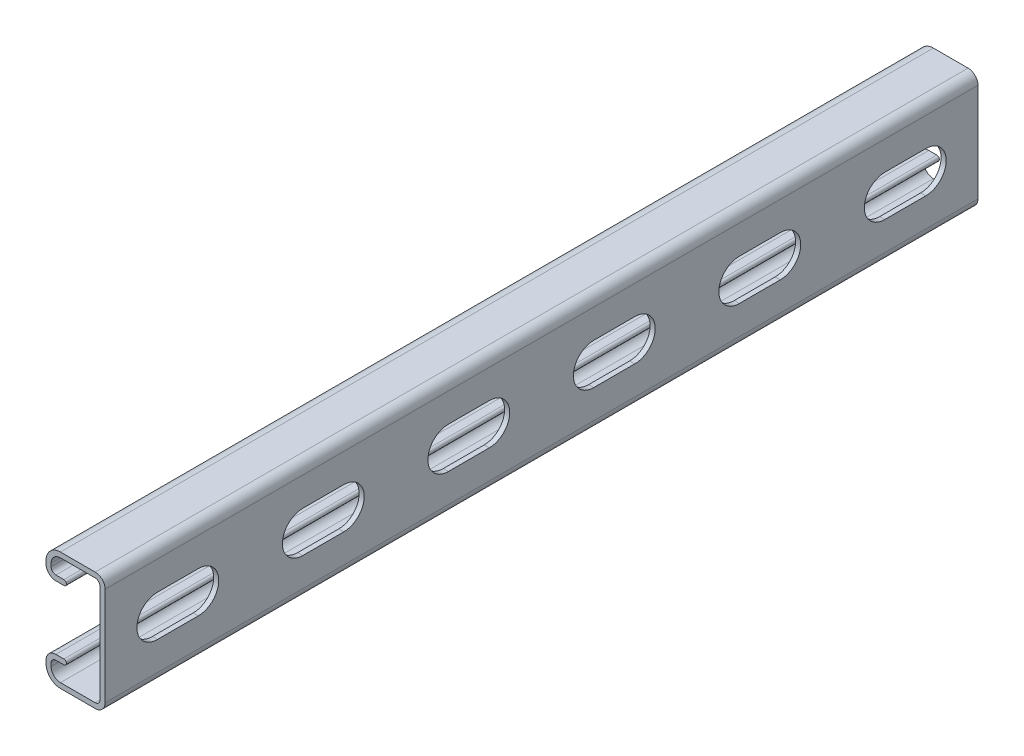
SolidWorks part; units mm, degrees
ref_plane "Front Plane" through (0, 0, 0) normal (0, 0, 1) x (1, 0, 0)
ref_plane "Top Plane" through (0, 0, 0) normal (0, 1, 0) x (1, 0, 0)
ref_plane "Right Plane" through (0, 0, 0) normal (1, 0, 0) x (0, 0, -1)
sketch "Sketch1" plane through (0, 0, 0) normal (0, 0, 1) x (1, 0, 0)
  line L0 (0, 0) -> (-20.6375, 0) construction
  line L3 (-20.6375, 20.6375) -> (0, 20.6375) construction
  line L4 (-20.6375, 20.6375) -> (-20.6375, -20.6375) construction
  line L5 (-20.6375, -20.6375) -> (0, -20.6375) construction
  line L6 (0, 20.6375) -> (0, -20.6375) construction
  line L7 (-15.5892, 20.6375) -> (-3.4607, 20.6375)
  line L8 (0, 17.1767) -> (0, -17.1767)
  line L9 (-1.778, -17.1767) -> (-1.778, 17.1767)
  line L10 (-3.4607, 18.8595) -> (-15.5892, 18.8595)
  line L11 (-20.6375, 15.5892) -> (-20.6375, 14.5732)
  line L12 (-17.1767, 11.1125) -> (-14.3891, 11.1125)
  line L14 (-14.3891, 12.8905) -> (-17.1767, 12.8905)
  line L15 (-18.8595, 14.5732) -> (-18.8595, 15.5892)
  line L16 (-18.8595, -14.5732) -> (-18.8595, -15.5892)
  line L17 (-14.3891, -12.8905) -> (-17.1767, -12.8905)
  line L18 (-17.1767, -11.1125) -> (-14.3891, -11.1125)
  line L19 (-20.6375, -15.5892) -> (-20.6375, -14.5732)
  line L20 (-3.4607, -18.8595) -> (-15.5892, -18.8595)
  line L21 (-15.5892, -20.6375) -> (-3.4607, -20.6375)
  line L22 (-1.778, -20.6375) -> (-1.778, 20.6375) construction
  arc A1 (0, 17.1767) -> (-3.4607, 20.6375) centre (-3.4607, 17.1767) ccw
  arc A2 (-1.778, 17.1767) -> (-3.4607, 18.8595) centre (-3.4607, 17.1767) ccw
  arc A4 (-15.5892, 20.6375) -> (-20.6375, 15.5892) centre (-15.5892, 15.5892) ccw
  arc A5 (-20.6375, 14.5732) -> (-17.1767, 11.1125) centre (-17.1767, 14.5732) ccw
  arc A6 (-14.3891, 11.1125) -> (-14.3891, 12.8905) centre (-14.3891, 12.0015) ccw
  arc A7 (-17.1767, 12.8905) -> (-18.8595, 14.5732) centre (-17.1767, 14.5732) cw
  arc A8 (-18.8595, 15.5892) -> (-15.5892, 18.8595) centre (-15.5892, 15.5892) cw
  arc A9 (-18.8595, -15.5892) -> (-15.5892, -18.8595) centre (-15.5892, -15.5892) ccw
  arc A10 (-17.1767, -12.8905) -> (-18.8595, -14.5732) centre (-17.1767, -14.5732) ccw
  arc A11 (-14.3891, -11.1125) -> (-14.3891, -12.8905) centre (-14.3891, -12.0015) cw
  arc A12 (-20.6375, -14.5732) -> (-17.1767, -11.1125) centre (-17.1767, -14.5732) cw
  arc A13 (-15.5892, -20.6375) -> (-20.6375, -15.5892) centre (-15.5892, -15.5892) cw
  arc A14 (-1.778, -17.1767) -> (-3.4607, -18.8595) centre (-3.4607, -17.1767) cw
  arc A15 (0, -17.1767) -> (-3.4607, -20.6375) centre (-3.4607, -17.1767) cw
  point P24 (0, 20.6375)
  point P65 (-1.778, 0)
  dimension "D1" = 3.4608
  dimension "D2" = 5.0482
  dimension "D3" = 3.4608
  dimension "Ht." = 20.6375
  dimension "Wd." = 41.275
  dimension "Thk." = 1.778
  dimension "D4" = 9.525
  dimension "D5" = 7.1374
extrude "Boss-Extrude1" add sketch "Sketch1" against normal blind 304.8
sketch "Sketch3" plane through (0, 0, 0) normal (1, 0, 0) x (0, 0, -1)
  line L0 (0, 0) -> (304.8, 0) construction
  point P2 (101.6, 0)
  point P3 (203.2, 0)
  dimension "D1" = 101.6
  dimension "D2" = 101.6
  dimension "D3" = 304.8
sketch "Sketch2" plane through (0, 0, 0) normal (1, 0, 0) x (0, 0, -1)
  line L0 (18.2562, 0) -> (32.5437, 0) construction
  line L1 (18.2562, 7.1437) -> (32.5437, 7.1437)
  line L2 (18.2562, -7.1437) -> (32.5437, -7.1437)
  line L3 (18.2562, 0) -> (0, 0) construction
  line L4 (25.4, 0) -> (76.2, 0) construction
  line L5 (0, -17.1767) -> (0, 17.1767) construction
  arc A0 (18.2562, 7.1437) -> (18.2562, -7.1437) centre (18.2562, 0) ccw
  arc A1 (32.5437, -7.1437) -> (32.5437, 7.1437) centre (32.5437, 0) ccw
  point P3 (25.4, 0)
  dimension "Hole to End" = 11.1125
  dimension "D2" = 25.4
extrude "Cut-Extrude1" cut sketch "Sketch2" against normal up to vertex (1.778 mm away) up to point (-1.778, 0, 0)
pattern_linear "LPattern1" count 6 spacing 50.8 along (0, 0, -1) of "Cut-Extrude1"
equation "\"D1@LPattern1\" = \"Slot Ctr.@Sketch2\""
equation "\"Hole Count@LPattern1\" = \"Lg.@Boss-Extrude1\" / \"D1@LPattern1\""
equation "\"D3@Sketch3\" = \"Lg.@Boss-Extrude1\""
